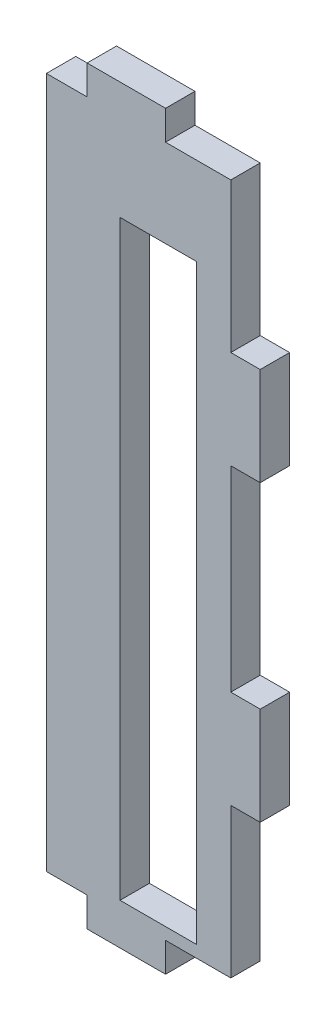
SolidWorks part; units mm, degrees
ref_plane "Front Plane" through (0, 0, 0) normal (0, 0, 1) x (1, 0, 0)
ref_plane "Top Plane" through (0, 0, 0) normal (0, 1, 0) x (1, 0, 0)
ref_plane "Right Plane" through (0, 0, 0) normal (1, 0, 0) x (0, 0, -1)
sketch "Sketch1" plane through (0, 0, 0) normal (0, 0, 1) x (1, 0, 0)
  line L0 (0, -10.75) -> (0, -24) construction
  line L2 (3, -10.75) -> (3, -0.75)
  line L5 (3, -29) -> (-24.3118, 47.5) construction
  line L6 (3, 47.5) -> (-24.3118, -29) construction
  line L7 (3, -10.75) -> (0, -10.75) construction
  line L8 (0, -10.75) -> (0, -24)
  line L9 (3, -10.75) -> (0, -10.75)
  line L10 (3, -0.75) -> (0, -0.75) construction
  line L11 (0, 19.25) -> (0, -0.75) construction
  line L12 (3, 19.25) -> (0, 19.25) construction
  line L13 (3, 29.25) -> (0, 29.25) construction
  line L14 (0, 42.5) -> (0, 29.25) construction
  line L15 (0, 47.5) -> (0, 42.5) construction
  line L16 (0, -24) -> (0, -29) construction
  line L17 (0, -24) -> (0, -26)
  line L18 (0, 44.5) -> (0, 42.5)
  line L19 (0, 42.5) -> (0, 29.25)
  line L20 (3, 29.25) -> (0, 29.25)
  line L21 (3, 19.25) -> (0, 19.25)
  line L22 (0, 19.25) -> (0, -0.75)
  line L23 (3, -0.75) -> (0, -0.75)
  line L24 (3, 19.25) -> (3, 29.25)
  line L25 (-10.6559, -35.4999) -> (-10.6559, 53.9999) construction
  line L26 (-3.5, -24.785) -> (-3.5, 35.54) construction
  line L36 (-3.5, 35.54) -> (-11.3, 35.54) construction
  line L37 (-11.3, -24.785) -> (-11.3, 35.54) construction
  line L38 (-3.5, -24.785) -> (-11.3, -24.785) construction
  line L39 (-3.5, -24.785) -> (-3.5, 35.54)
  line L40 (-3.5, 35.54) -> (-11.3, 35.54)
  line L41 (-11.3, -24.785) -> (-11.3, 35.54)
  line L42 (-3.5, -24.785) -> (-11.3, -24.785)
  line L52 (0, -26) -> (-2, -26)
  line L53 (-19.3118, -26) -> (-21.3118, -26)
  line L54 (-19.3118, -26) -> (-2, -26)
  line L56 (0, 44.5) -> (-21.3118, 44.5)
  line L57 (-21.3118, -26) -> (-21.3118, 44.5)
  point P4 (-10.6559, 9.25)
  point P18 (-10.6559, 9.25)
extrude "Boss-Extrude1" add sketch "Sketch1" along normal blind 3
sketch "Sketch2" plane through (0, 0, 3) normal (0, 0, 1) x (1, 0, 0)
  line L0 (0, 44.5) -> (-21.3118, 44.5) construction
  line L1 (-21.3118, -26) -> (-18.8118, -26)
  line L2 (-21.3118, -26) -> (-21.3118, 44.5)
  line L3 (-21.3118, 44.5) -> (-18.8118, 44.5)
  line L4 (-18.8118, -26) -> (-18.8118, 44.5)
  line L5 (-21.3118, -26) -> (-18.8118, 44.5) construction
  line L6 (-21.3118, 44.5) -> (-18.8118, -26) construction
  point P4 (-20.0618, 9.25)
  dimension "D1" = 2.5
extrude "Cut-Extrude1" cut sketch "Sketch2" against normal blind 3
sketch "Sketch3" plane through (0, 0, 3) normal (0, 0, 1) x (1, 0, 0)
  line L0 (-14.6559, -26) -> (-14.6559, -29) construction
  line L1 (-6.6559, -26) -> (-6.6559, -29) construction
  line L2 (-14.6559, -26) -> (-14.6559, -29)
  line L3 (-6.6559, -26) -> (-6.6559, -29)
  line L4 (-6.6559, -26) -> (-14.6559, -26)
  line L5 (-6.6559, -29) -> (-14.6559, -29)
  line L6 (0, 9.25) -> (-36.8131, 9.25) construction
  line L7 (0, -0.75) -> (0, 19.25) construction
  line L8 (-6.6559, 47.5) -> (-14.6559, 47.5)
  line L9 (-6.6559, 44.5) -> (-14.6559, 44.5)
  line L10 (-6.6559, 44.5) -> (-6.6559, 47.5)
  line L11 (-14.6559, 44.5) -> (-14.6559, 47.5)
extrude "Boss-Extrude2" add sketch "Sketch3" against normal blind 3
